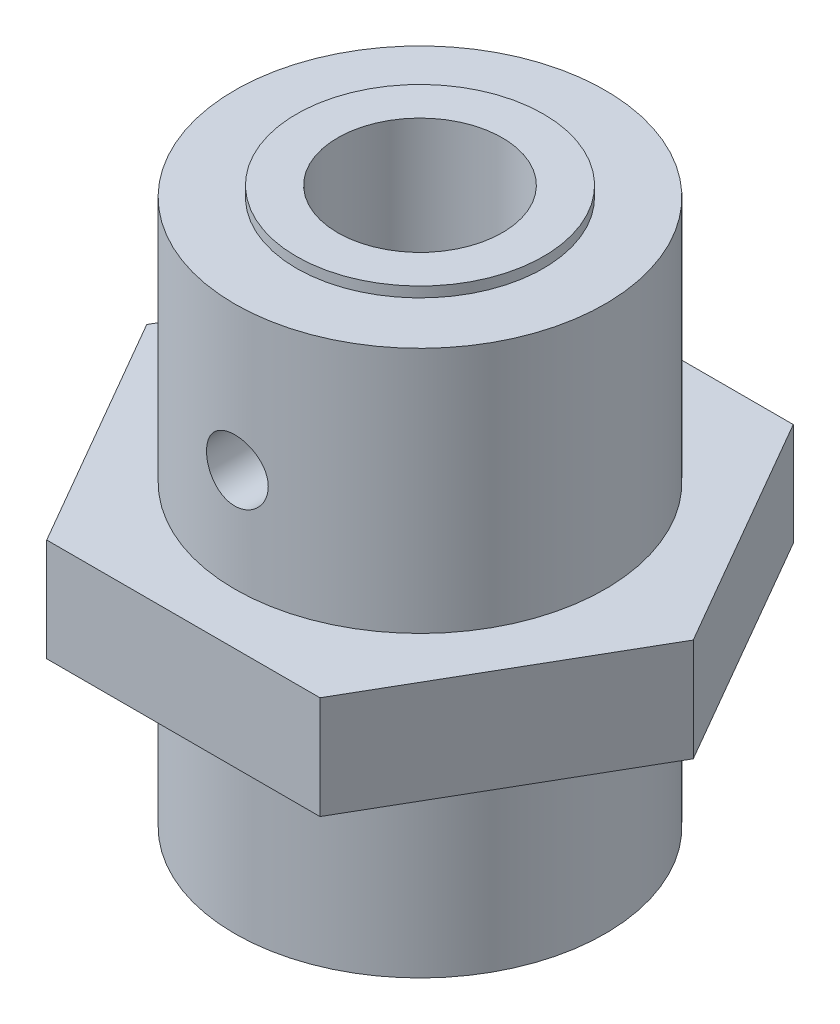
SolidWorks part; units mm, degrees
material "1060 Alloy"
ref_plane "Front Plane" through (0, 0, 0) normal (0, 0, 1) x (1, 0, 0)
ref_plane "Top Plane" through (0, 0, 0) normal (0, 1, 0) x (1, 0, 0)
ref_plane "Right Plane" through (0, 0, 0) normal (1, 0, 0) x (0, 0, -1)
sketch "Sketch1" plane through (0, 0, 0) normal (0, 1, 0) x (1, 0, 0)
  circle A0 centre (0, 0) radius 9
  circle A1 centre (0, 0) radius 4
extrude "Boss-Extrude1" add sketch "Sketch1" along normal blind 27
sketch "Sketch2" plane through (0, 27, 0) normal (0, 1, 0) x (1, 0, 0)
  circle A0 centre (0, 0) radius 6
  circle A1 centre (0, 0) radius 9
extrude "Cut-Extrude1" cut sketch "Sketch2" against normal blind 0.5
sketch "Sketch3" plane through (0, 0, 0) normal (0, 0, 1) x (1, 0, 0)
  line L0 (0, 0) -> (0, 27) construction
  line L1 (4, 27) -> (-4, 27) construction
  line L2 (9, 26.5) -> (-9, 26.5) construction
  circle A0 centre (0, 19.5) radius 1.5
  dimension "D1" = 7
  dimension "D2" = 3
extrude "Cut-Extrude2" cut sketch "Sketch3" against normal through all both and the other way through all
ref_plane "Plane1" through (0, 14.5, 0) normal (0, 1, 0) x (1, 0, 0)
sketch "Sketch4" plane through (0, 14.5, 0) normal (0, 1, 0) x (1, 0, 0)
  line L1 (13.2791, 0) -> (6.6395, 11.5)
  line L2 (6.6395, 11.5) -> (-6.6395, 11.5)
  line L3 (-6.6395, 11.5) -> (-13.2791, 0)
  line L4 (-13.2791, 0) -> (-6.6395, -11.5)
  line L5 (-6.6395, -11.5) -> (6.6395, -11.5)
  line L6 (6.6395, -11.5) -> (13.2791, 0)
  circle A0 centre (0, 0) radius 4
  circle A1 centre (0, 0) radius 11.5 construction
  dimension "D2" = 8
  dimension "D1" = 23
extrude "Boss-Extrude2" add sketch "Sketch4" against normal blind 5
